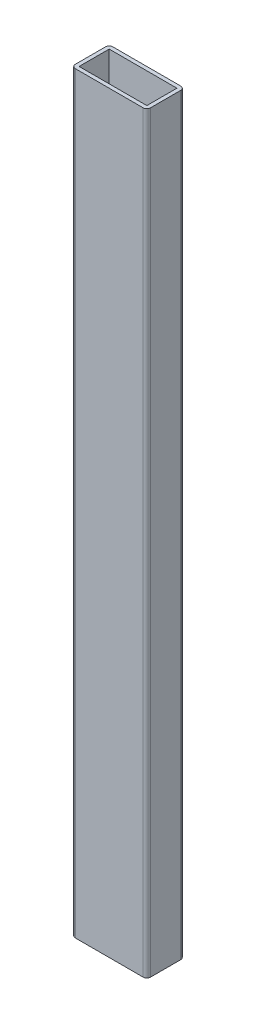
SolidWorks part; units mm, degrees
ref_plane "Спереди" through (0, 0, 0) normal (0, 0, 1) x (1, 0, 0)
ref_plane "Сверху" through (0, 0, 0) normal (0, 1, 0) x (1, 0, 0)
ref_plane "Справа" through (0, 0, 0) normal (1, 0, 0) x (0, 0, -1)
sketch "Эскиз1" plane through (0, 0, 0) normal (0, 1, 0) x (1, 0, 0)
  line L1 (-18, 10) -> (18, 10)
  line L2 (-20, 8) -> (-20, -8)
  line L3 (-18, -10) -> (18, -10)
  line L4 (20, 8) -> (20, -8)
  line L5 (-20, 10) -> (20, -10) construction
  line L6 (-20, -10) -> (20, 10) construction
  arc A0 (-20, -8) -> (-18, -10) centre (-18, -8) ccw
  arc A1 (18, -10) -> (20, -8) centre (18, -8) ccw
  arc A2 (18, 10) -> (20, 8) centre (18, 8) cw
  arc A3 (-18, 10) -> (-20, 8) centre (-18, 8) ccw
  point P0 (0, 0)
  dimension "D1" = 2
extrude "Вытянуть-Тонкостенный1" add sketch "Эскиз1" along normal blind 400 thin
